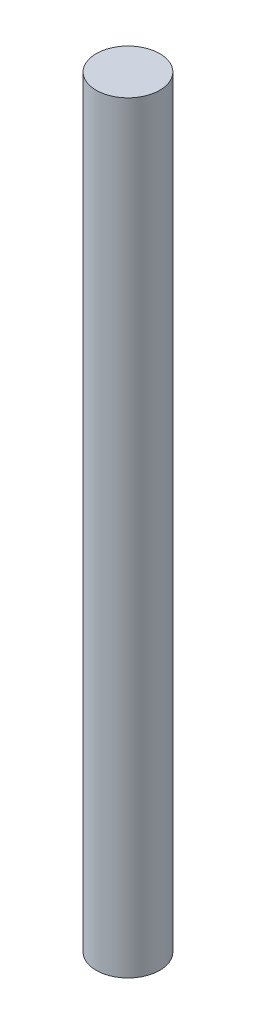
SolidWorks part; units mm, degrees
material "1023 Carbon Steel Sheet (SS)"
ref_plane "Front Plane" through (0, 0, 0) normal (0, 0, 1) x (1, 0, 0)
ref_plane "Top Plane" through (0, 0, 0) normal (0, 1, 0) x (1, 0, 0)
ref_plane "Right Plane" through (0, 0, 0) normal (1, 0, 0) x (0, 0, -1)
sketch "Sketch1" plane through (0, 0, 0) normal (0, 1, 0) x (1, 0, 0)
  circle A0 centre (0, 0) radius 1.5
extrude "Boss-Extrude1" add sketch "Sketch1" along normal blind 36
